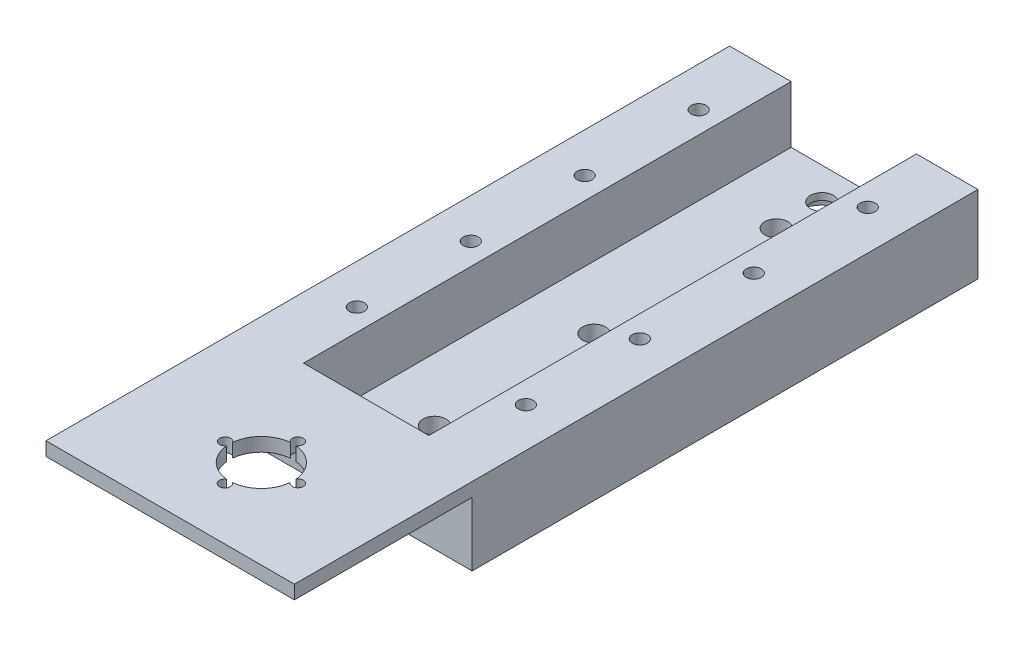
SolidWorks part; units mm, degrees
ref_plane "Front Plane" through (0, 0, 0) normal (0, 0, 1) x (1, 0, 0)
ref_plane "Top Plane" through (0, 0, 0) normal (0, 1, 0) x (1, 0, 0)
ref_plane "Right Plane" through (0, 0, 0) normal (1, 0, 0) x (0, 0, -1)
sketch "Sketch1" plane through (0, 0, 0) normal (0, 1, 0) x (1, 0, 0)
  line L1 (-40.6495, -11.3707) -> (13.8505, -11.3707)
  line L2 (-40.6495, -11.3707) -> (-40.6495, 99.6293)
  line L3 (-40.6495, 99.6293) -> (13.8505, 99.6293)
  line L4 (13.8505, -11.3707) -> (13.8505, 99.6293)
  dimension "D1" = 54.5
  dimension "D2" = 111
extrude "Boss-Extrude1" add sketch "Sketch1" along normal blind 4.5
sketch "Sketch2" plane through (0, 4.5, 0) normal (0, 1, 0) x (1, 0, 0)
  line L0 (13.8505, 99.6293) -> (-40.6495, 99.6293) construction
  line L1 (0.3505, 99.6293) -> (13.8505, 99.6293)
  line L2 (0.3505, 99.6293) -> (0.3505, -11.3707)
  line L3 (0.3505, -11.3707) -> (13.8505, -11.3707)
  line L4 (13.8505, 99.6293) -> (13.8505, -11.3707)
  line L5 (-40.6495, -11.3707) -> (13.8505, -11.3707) construction
  line L6 (-40.6495, 99.6293) -> (-27.1495, 99.6293)
  line L7 (-40.6495, 99.6293) -> (-40.6495, -11.3707)
  line L8 (-40.6495, -11.3707) -> (-27.1495, -11.3707)
  line L9 (-27.1495, 99.6293) -> (-27.1495, -11.3707)
  dimension "D1" = 13.5
  dimension "D2" = 13.5
extrude "Boss-Extrude2" add sketch "Sketch2" along normal blind 12.5 contours L7 L6 L9 L8 | L2 L1 L4 L3
hole_wizard "M4x0.7 Tapped Hole1" positions "3DSketch1" profile "Sketch3" tap size "M4x0.7" standard "ANSI Metric" end condition through all
sketch3d "3DSketch1"
  line L0 (-40.6495, 17, -99.6293) -> (-27.1495, 17, -99.6293) construction
  line L1 (-40.6495, 17, -99.6293) -> (-40.6495, 17, 11.3707) construction
  line L2 (-40.6495, 17, 11.3707) -> (-27.1495, 17, 11.3707) construction
  line L3 (0.3505, 17, -99.6293) -> (13.8505, 17, -99.6293) construction
  line L4 (13.8505, 17, -99.6293) -> (13.8505, 17, 11.3707) construction
  point P0 (-31.9495, 17, -9.1293)
  point P2 (-31.9495, 17, -34.1293)
  point P4 (-31.9495, 17, -59.1293)
  point P6 (-31.9495, 17, -84.1293)
  point P8 (5.1505, 17, -9.1293)
  point P10 (5.1505, 17, -34.1293)
  point P12 (5.1505, 17, -59.1293)
  point P14 (5.1505, 17, -84.1293)
  dimension "D1" = 15.5
  dimension "D2" = 8.7
  dimension "D3" = 25
  dimension "D4" = 8.7
  dimension "D5" = 25
  dimension "D6" = 8.7
  dimension "D7" = 25
  dimension "D8" = 8.7
  dimension "D9" = 20.5
  dimension "D10" = 15.5
  dimension "D11" = 8.7
  dimension "D12" = 25
  dimension "D13" = 8.7
  dimension "D14" = 25
  dimension "D15" = 8.7
  dimension "D16" = 8.7
  dimension "D17" = 25
sketch "Sketch3" plane through (-31.9495, 17, -9.1293) normal (1, 0, 0) x (0, 0, 1)
  line L0 (0, 0) -> (0, 17)
  line L1 (0, 17) -> (1.65, 17)
  line L2 (1.65, 17) -> (1.65, 0)
  line L5 (1.65, 0) -> (0, 0)
  line L11 (0, -6.35) -> (0, 107.95) construction
  dimension "Thru Tap Drill Dia." = 3.3
  dimension "Thru Tap Drill Depth" = 17
cosmetic thread "Hole Thread1" parameters "D2"=4
cosmetic thread "Hole Thread2" parameters "D2"=4
cosmetic thread "Hole Thread3" parameters "D2"=4
cosmetic thread "Hole Thread4" parameters "D2"=4
cosmetic thread "Hole Thread5" parameters "D2"=4
cosmetic thread "Hole Thread6" parameters "D2"=4
cosmetic thread "Hole Thread7" parameters "D2"=4
cosmetic thread "Hole Thread8" parameters "D2"=4
sketch "Sketch6" plane through (-27.1495, 0, 0) normal (1, 0, 0) x (0, 0, -1)
  line L0 (99.6293, 4.5) -> (-11.3707, 4.5) construction
  line L1 (-11.3707, 17) -> (-7.3707, 17)
  line L2 (-11.3707, 17) -> (-11.3707, 4.5)
  line L3 (-11.3707, 4.5) -> (-7.3707, 4.5)
  line L4 (-7.3707, 17) -> (-7.3707, 4.5)
  dimension "D1" = 4
extrude "Boss-Extrude3" add sketch "Sketch6" along normal blind 37
sketch "Sketch7" plane through (0, 0, 11.3707) normal (0, 0, 1) x (1, 0, 0)
  line L0 (13.8505, 17) -> (13.8505, 0) construction
  line L1 (-40.6495, 17) -> (13.8505, 17)
  line L2 (-40.6495, 17) -> (-40.6495, 14)
  line L3 (-40.6495, 14) -> (13.8505, 14)
  line L4 (13.8505, 17) -> (13.8505, 14)
  dimension "D1" = 3
extrude "Boss-Extrude5" add sketch "Sketch7" along normal blind 39
sketch "Sketch8" plane through (0, 17, 0) normal (0, 1, 0) x (1, 0, 0)
  line L1 (-40.6495, 99.6293) -> (-40.6495, -50.3707) construction
  circle A0 centre (-12.8995, -30.8707) radius 7
  dimension "D1" = 19.5
  dimension "D2" = 27.75
extrude "Cut-Extrude1" cut sketch "Sketch8" against normal blind 3 contours A0
hole_wizard "M2 Clearance Hole1" positions "3DSketch2" profile "Sketch9" hole size "M2" standard "ANSI Metric" end condition through all
sketch3d "3DSketch2"
  line L0 (13.8505, 17, 50.3707) -> (-40.6495, 17, 50.3707) construction
  line L1 (13.8505, 17, -99.6293) -> (13.8505, 17, 50.3707) construction
  point P0 (-20.8714, 17, 30.8479)
  point P2 (-12.8995, 17, 22.8707)
  point P4 (-12.8995, 17, 38.8707)
  point P12 (-4.9305, 17, 30.8451)
  dimension "D1" = 11.5
  dimension "D2" = 16
  dimension "D3" = 26.75
  dimension "D4" = 26.75
  dimension "D5" = 11.31
  dimension "D6" = 11.31
sketch "Sketch9" plane through (-20.8714, 17, 30.8479) normal (1, 0, 0) x (0, 0, 1)
  line L0 (0, 0) -> (0, 17)
  line L1 (0, 17) -> (1.2, 17)
  line L2 (1.2, 17) -> (1.2, 0)
  line L5 (1.2, 0) -> (0, 0)
  line L11 (0, -6.35) -> (0, 107.95) construction
  dimension "Thru Hole Dia." = 2.4
  dimension "Thru Hole Depth" = 17
hole_wizard "#8 (0.199) Diameter Hole1" positions "3DSketch4" profile "Sketch10" hole size "#8" standard "Progressive" end condition through all
sketch3d "3DSketch4"
  line L4 (0.3505, 4.5, -99.6293) -> (0.3505, 4.5, 7.3707) construction
  line L6 (0.3505, 4.5, 7.3707) -> (-27.1495, 4.5, 7.3707) construction
  line L7 (0.3505, 4.5, -99.6293) -> (-27.1495, 4.5, -99.6293) construction
  point P0 (-13.3995, 4.5, 2.3707)
  point P2 (-13.3995, 4.5, -7.6293)
  point P4 (-13.3995, 4.5, -42.6293)
  point P6 (-13.3995, 4.5, -82.6293)
  point P8 (-13.3995, 4.5, -92.6293)
  dimension "D1" = 13.75
  dimension "D2" = 13.75
  dimension "D4" = 13.75
  dimension "D3" = 13.75
  dimension "D5" = 13.75
  dimension "D6" = 5
  dimension "10" = 10
  dimension "D7" = 7
  dimension "D8" = 10
  dimension "D9" = 35
sketch "Sketch10" plane through (-13.3995, 4.5, 2.3707) normal (1, 0, 0) x (0, 0, 1)
  line L0 (0, 0) -> (0, 4.5)
  line L1 (0, 4.5) -> (2.5273, 4.5)
  line L2 (2.5273, 4.5) -> (2.5273, 0)
  line L5 (2.5273, 0) -> (0, 0)
  line L11 (0, -6.35) -> (0, 107.95) construction
  dimension "Thru Hole Dia." = 5.0546
  dimension "Thru Hole Depth" = 4.5
sketch "Sketch12" plane through (0, 0, 0) normal (0, -1, 0) x (-1, 0, 0)
  circle A2 centre (13.3995, 92.6293) radius 5.5
extrude "Cut-Extrude3" cut sketch "Sketch12" against normal blind 3
